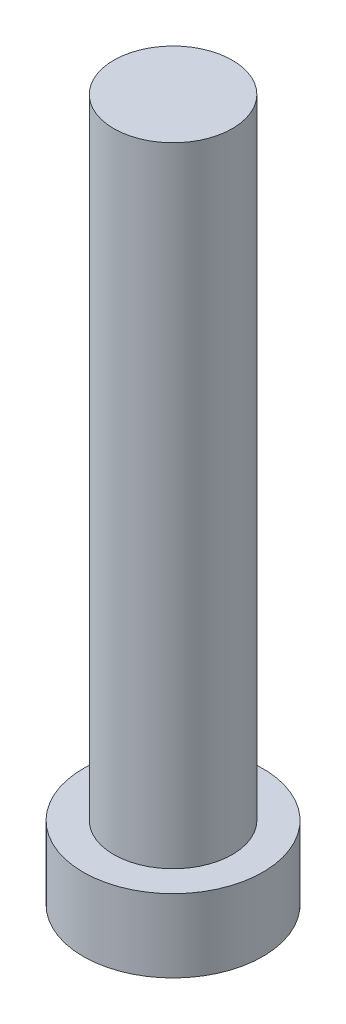
SolidWorks part; units mm, degrees
ref_plane "Front Plane" through (0, 0, 0) normal (0, 0, 1) x (1, 0, 0)
ref_plane "Top Plane" through (0, 0, 0) normal (0, 1, 0) x (1, 0, 0)
ref_plane "Right Plane" through (0, 0, 0) normal (1, 0, 0) x (0, 0, -1)
sketch "Sketch1" plane through (0, 0, 0) normal (0, 1, 0) x (1, 0, 0)
  circle A0 centre (0, 0) radius 5
  dimension "D1" = 10
extrude "Boss-Extrude1" add sketch "Sketch1" along normal blind 4.064
sketch "Sketch2" plane through (0, 4.064, 0) normal (0, 1, 0) x (1, 0, 0)
  circle A0 centre (0, 0) radius 3.3
  dimension "D1" = 6.6
extrude "Boss-Extrude2" add sketch "Sketch2" along normal blind 39.0652 from surface at -4.064 starting at face at (0, 0, 5)
